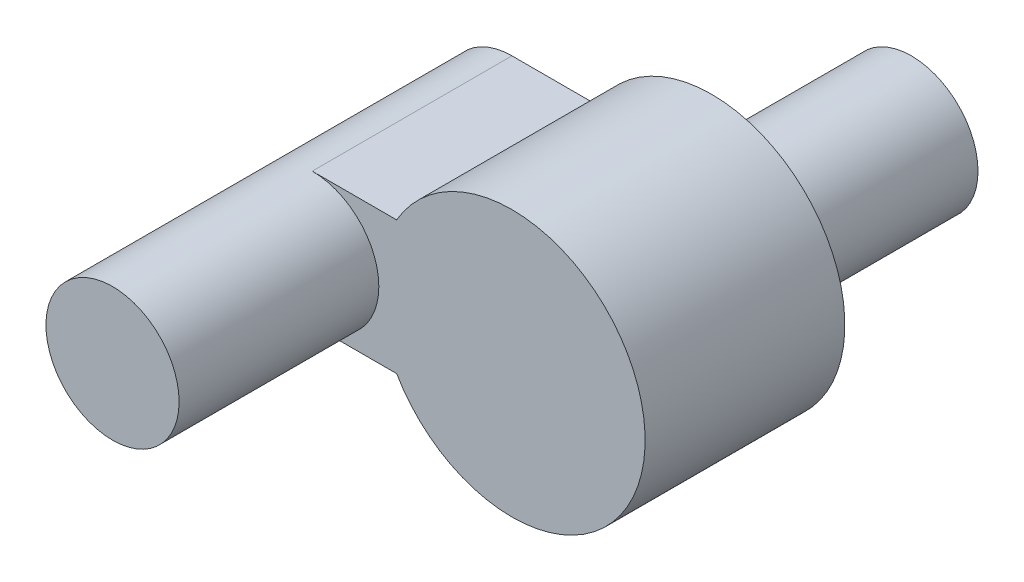
SolidWorks part; units mm, degrees
ref_plane "Спереди" through (0, 0, 0) normal (0, 0, 1) x (1, 0, 0)
ref_plane "Сверху" through (0, 0, 0) normal (0, 1, 0) x (1, 0, 0)
ref_plane "Справа" through (0, 0, 0) normal (1, 0, 0) x (0, 0, -1)
other "Configuration Table"
sketch "Sketch1" plane through (0, 0, 0) normal (0, 0, 1) x (1, 0, 0)
  line L0 (-0.8022, 3.8198) -> (-10.8725, 3.8198) construction
  line L1 (-10.074, 4.8198) -> (-8.8061, 4.8198)
  line L7 (-10.074, 2.8198) -> (-8.8061, 2.8198)
  arc A2 (-10.074, 4.8198) -> (-10.074, 2.8198) centre (-10.074, 3.8198) ccw
  arc A3 (-9.074, 3.8198) -> (-10.074, 4.8198) centre (-10.074, 3.8198) ccw construction
  arc A4 (-10.074, 2.8198) -> (-9.074, 3.8198) centre (-10.074, 3.8198) ccw construction
  arc A5 (-8.8061, 2.8198) -> (-8.8061, 4.8198) centre (-7.074, 3.8198) ccw
  arc A6 (-8.8061, 4.8198) -> (-9.074, 3.8198) centre (-7.074, 3.8198) ccw construction
  arc A7 (-9.074, 3.8198) -> (-8.8061, 2.8198) centre (-7.074, 3.8198) ccw construction
  point P0 (-6.8133, 3.8198)
  dimension "D2" = 2
  dimension "D1" = 4
  dimension "D3" = 3
  dimension "D4" = 2
extrude "Boss-Extrude1" add sketch "Sketch1" along normal blind 3
ref_plane "Plane1" through (0, 0, 3) normal (0, 0, 1) x (1, 0, 0)
sketch "Sketch2" plane through (0, 0, 3) normal (0, 0, 1) x (1, 0, 0)
  circle A0 centre (-10.074, 3.8198) radius 1
  arc A1 (-10.074, 4.8198) -> (-10.074, 2.8198) centre (-10.074, 3.8198) ccw construction
extrude "Boss-Extrude2" add sketch "Sketch2" along normal blind 3
ref_plane "Plane2" through (0, 0, 0) normal (0, 0, -1) x (-1, 0, 0)
sketch "Sketch3" plane through (0, 0, 0) normal (0, 0, -1) x (-1, 0, 0)
  circle A0 centre (7.074, 3.8198) radius 1
  circle A1 centre (10.074, 3.8198) radius 1 construction
extrude "Boss-Extrude3" add sketch "Sketch3" along normal blind 3
equation "\"R small\"= 2"
equation "\"R big\"= 4"
equation "\"width\"= 0.6"
equation "\"border width\"= 1"
equation "\"D4@Sketch1\"=\"R small\""
equation "\"D2@Sketch1\"=\"R small\""
